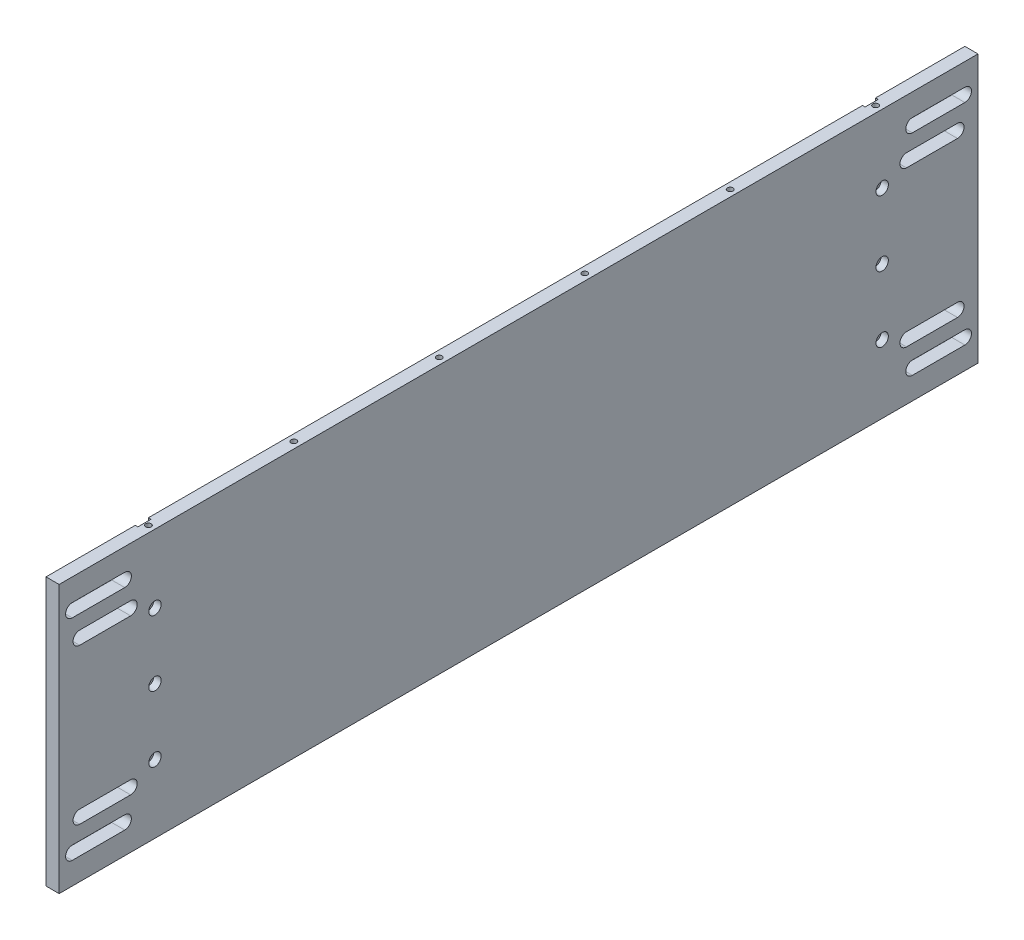
SolidWorks part; units mm, degrees
material "6061 Alloy"
ref_plane "Front Plane" through (0, 0, 0) normal (0, 0, 1) x (1, 0, 0)
ref_plane "Top Plane" through (0, 0, 0) normal (0, 1, 0) x (1, 0, 0)
ref_plane "Right Plane" through (0, 0, 0) normal (1, 0, 0) x (0, 0, -1)
sketch "Sketch1" plane through (0, 0, 0) normal (1, 0, 0) x (0, 0, -1)
  line L1 (0, 0) -> (444.5, 0)
  line L2 (0, 0) -> (0, 129.54)
  line L3 (0, 129.54) -> (444.5, 129.54)
  line L4 (444.5, 0) -> (444.5, 129.54)
  dimension "D1" = 444.5
  dimension "D2" = 129.54
extrude "Boss-Extrude1" add sketch "Sketch1" along normal blind 6.35
hole_wizard "CBORE for #6 Socket Head Cap Screw1" positions "Sketch15" profile "Sketch14" counterbore size "#6" standard "ANSI Inch" end condition through all
sketch "Sketch15" plane through (6.35, 0, 0) normal (1, 0, 0) x (0, 0, -1)
  line L1 (444.5, 129.54) -> (0, 129.54) construction
  line L3 (222.25, 129.54) -> (222.25, 0) construction
  line L4 (0, 0) -> (444.5, 0) construction
  line L6 (46.355, 96.52) -> (46.355, 33.02) construction
  line L8 (398.145, 96.52) -> (398.145, 33.02) construction
  line L9 (444.5, 64.77) -> (0, 64.77) construction
  line L10 (444.5, 0) -> (444.5, 129.54) construction
  line L11 (0, 129.54) -> (0, 0) construction
  point P0 (46.355, 64.77)
  point P8 (398.145, 64.77)
  point P13 (46.355, 96.52)
  point P15 (46.355, 33.02)
  point P17 (398.145, 96.52)
  point P19 (398.145, 33.02)
  dimension "D1" = 175.895
  dimension "D3" = 175.895
  dimension "D4" = 31.75
  dimension "D5" = 31.75
  dimension "D6" = 31.75
  dimension "D7" = 31.75
sketch "Sketch14" plane through (6.35, 64.77, -46.355) normal (0, 1, 0) x (0, 0, -1)
  line L0 (0, 0) -> (0, 6.35)
  line L1 (0, 6.35) -> (1.8288, 6.35)
  line L3 (1.8288, 6.35) -> (1.8288, 3.5052)
  line L4 (1.8288, 3.5052) -> (3, 3.5052)
  line L5 (3, 3.5052) -> (3, 0)
  line L7 (3, 0) -> (0, 0)
  line L11 (0, -6.35) -> (0, 107.95) construction
  dimension "Thru Hole Dia." = 3.6576
  dimension "Thru Hole Depth" = 6.35
  dimension "C'Bore Dia." = 6
  dimension "C'Bore Depth" = 3.5052
sketch "Sketch16" plane through (6.35, 0, 0) normal (1, 0, 0) x (0, 0, -1)
  line L0 (222.25, 129.54) -> (222.25, 0) construction
  line L1 (444.5, 129.54) -> (0, 129.54) construction
  line L2 (0, 0) -> (444.5, 0) construction
  line L3 (6.35, 115.57) -> (31.75, 115.57) construction
  line L4 (0, 129.54) -> (0, 0) construction
  line L5 (0, 64.77) -> (444.5, 64.77) construction
  line L6 (444.5, 0) -> (444.5, 129.54) construction
  line L7 (6.35, 118.7704) -> (31.75, 118.7704)
  line L8 (6.35, 112.3696) -> (31.75, 112.3696)
  line L9 (434.5817, 27.27) -> (409.9183, 27.27) construction
  line L10 (434.5817, 24.095) -> (409.9183, 24.095)
  line L11 (434.5817, 30.445) -> (409.9183, 30.445)
  line L12 (434.5817, 102.27) -> (409.9183, 102.27) construction
  line L13 (434.5817, 105.445) -> (409.9183, 105.445)
  line L14 (434.5817, 99.095) -> (409.9183, 99.095)
  line L15 (6.35, 13.97) -> (31.75, 13.97) construction
  line L16 (6.35, 10.7696) -> (31.75, 10.7696)
  line L17 (6.35, 17.1704) -> (31.75, 17.1704)
  line L18 (438.15, 115.57) -> (412.75, 115.57) construction
  line L19 (438.15, 118.7704) -> (412.75, 118.7704)
  line L20 (438.15, 112.3696) -> (412.75, 112.3696)
  line L21 (9.9183, 102.27) -> (34.5817, 102.27) construction
  line L22 (9.9183, 105.445) -> (34.5817, 105.445)
  line L23 (9.9183, 99.095) -> (34.5817, 99.095)
  line L24 (9.9183, 27.27) -> (34.5817, 27.27) construction
  line L25 (9.9183, 24.095) -> (34.5817, 24.095)
  line L26 (9.9183, 30.445) -> (34.5817, 30.445)
  line L27 (438.15, 13.97) -> (412.75, 13.97) construction
  line L28 (438.15, 10.7696) -> (412.75, 10.7696)
  line L29 (438.15, 17.1704) -> (412.75, 17.1704)
  arc A0 (6.35, 118.7704) -> (6.35, 112.3696) centre (6.35, 115.57) ccw
  arc A1 (31.75, 112.3696) -> (31.75, 118.7704) centre (31.75, 115.57) ccw
  arc A2 (434.5817, 24.095) -> (434.5817, 30.445) centre (434.5817, 27.27) ccw
  arc A3 (409.9183, 30.445) -> (409.9183, 24.095) centre (409.9183, 27.27) ccw
  arc A4 (434.5817, 105.445) -> (434.5817, 99.095) centre (434.5817, 102.27) cw
  arc A5 (409.9183, 99.095) -> (409.9183, 105.445) centre (409.9183, 102.27) cw
  arc A6 (6.35, 10.7696) -> (6.35, 17.1704) centre (6.35, 13.97) cw
  arc A7 (31.75, 17.1704) -> (31.75, 10.7696) centre (31.75, 13.97) cw
  arc A8 (438.15, 118.7704) -> (438.15, 112.3696) centre (438.15, 115.57) cw
  arc A9 (412.75, 112.3696) -> (412.75, 118.7704) centre (412.75, 115.57) cw
  arc A10 (9.9183, 105.445) -> (9.9183, 99.095) centre (9.9183, 102.27) ccw
  arc A11 (34.5817, 99.095) -> (34.5817, 105.445) centre (34.5817, 102.27) ccw
  arc A12 (9.9183, 24.095) -> (9.9183, 30.445) centre (9.9183, 27.27) cw
  arc A13 (34.5817, 30.445) -> (34.5817, 24.095) centre (34.5817, 27.27) cw
  arc A14 (438.15, 10.7696) -> (438.15, 17.1704) centre (438.15, 13.97) ccw
  arc A15 (412.75, 17.1704) -> (412.75, 10.7696) centre (412.75, 13.97) ccw
  point P14 (19.05, 115.57)
  point P20 (422.25, 27.27)
  point P28 (422.25, 102.27)
  point P35 (19.05, 13.97)
  point P42 (425.45, 115.57)
  point P49 (22.25, 102.27)
  point P56 (22.25, 27.27)
  point P63 (425.45, 13.97)
  dimension "D1" = 203.2
  dimension "D2" = 200
  dimension "D3" = 50.8
  dimension "D4" = 37.5
  dimension "D5" = 25.4
  dimension "D6" = 24.6634
extrude "Cut-Extrude1" cut sketch "Sketch16" against normal through all
hole_wizard "Tap Drill for #6-32 Tap1" positions "Sketch17" profile "Sketch18" hole size "#6-32" standard "ANSI Inch"
sketch "Sketch17" plane through (-408.1871, 129.54, -132.107) normal (0, 1, 0) x (0, 0, -1)
  point P0 (-85.752, -59.5721)
  point P3 (-15.394, -59.5721)
  point P6 (54.964, -59.5721)
  point P9 (125.322, -59.5721)
  point P12 (195.68, -59.5721)
  point P15 (266.038, -59.5721)
  point P18 (266.038, -129.9301)
  point P21 (266.038, -200.2881)
  point P24 (266.038, -270.6461)
  point P27 (266.038, -341.0041)
  point P30 (266.038, -411.3621)
  point P33 (195.68, -411.3621)
  point P36 (125.322, -411.3621)
  point P39 (54.964, -411.3621)
  point P42 (-15.394, -411.3621)
  point P45 (-85.752, -411.3621)
  point P48 (-85.752, -341.0041)
  point P51 (-85.752, -270.6461)
  point P54 (-85.752, -200.2881)
  point P57 (-85.752, -129.9301)
sketch "Sketch18" plane through (-348.615, 129.54, -46.355) normal (1, 0, 0) x (0, 0, 1)
  line L0 (0, 0) -> (0, 18.5927)
  line L1 (0, 18.5927) -> (1.3525, 17.78)
  line L2 (1.3525, 17.78) -> (1.3525, 0)
  line L3 (1.3525, 0) -> (0, 0)
  line L4 (0, 18.5927) -> (-1.3525, 17.78) construction
  line L5 (0, -6.35) -> (0, 107.95) construction
  dimension "Hole Dia." = 2.7051
  dimension "Hole Depth" = 17.78
  dimension "Drill Angle" = 118
hole_wizard "Tap Drill for #6-32 Tap2" positions "Sketch19" profile "Sketch20" hole size "#6-32" standard "ANSI Inch"
sketch "Sketch19" plane through (62.7725, 0, -312.3676) normal (0, -1, 0) x (0, 0, -1)
  point P0 (85.752, -411.3621)
  point P3 (15.394, -411.3621)
  point P6 (-54.964, -411.3621)
  point P9 (-125.322, -411.3621)
  point P12 (-195.68, -411.3621)
  point P15 (-266.038, -411.3621)
  point P18 (-266.038, -341.0041)
  point P21 (-266.038, -270.6461)
  point P24 (-266.038, -200.2881)
  point P27 (-266.038, -129.9301)
  point P30 (-266.038, -59.5721)
  point P33 (-195.68, -59.5721)
  point P36 (-125.322, -59.5721)
  point P39 (-54.964, -59.5721)
  point P42 (15.394, -59.5721)
  point P45 (85.752, -59.5721)
  point P48 (85.752, -130.0063)
  point P51 (85.752, -200.3643)
  point P54 (85.752, -270.7223)
  point P57 (85.752, -341.0803)
sketch "Sketch20" plane through (-348.5896, 0, -398.1196) normal (1, 0, 0) x (0, 0, -1)
  line L0 (0, 0) -> (0, 18.5927)
  line L1 (0, 18.5927) -> (1.3525, 17.78)
  line L2 (1.3525, 17.78) -> (1.3525, 0)
  line L3 (1.3525, 0) -> (0, 0)
  line L4 (0, 18.5927) -> (-1.3525, 17.78) construction
  line L5 (0, -6.35) -> (0, 107.95) construction
  dimension "Hole Dia." = 2.7051
  dimension "Hole Depth" = 17.78
  dimension "Drill Angle" = 118
sketch "Sketch21" plane through (0, 0, 0) normal (-1, 0, 0) x (0, 0, 1)
  line L0 (-444.5, 129.54) -> (0, 129.54) construction
  line L1 (-401.32, 0) -> (-394.97, 0)
  line L2 (-401.32, 0) -> (-401.32, 129.54)
  line L3 (-401.32, 129.54) -> (-394.97, 129.54)
  line L4 (-394.97, 0) -> (-394.97, 129.54)
  line L5 (-401.32, 0) -> (-394.97, 129.54) construction
  line L6 (-401.32, 129.54) -> (-394.97, 0) construction
  line L8 (-43.18, 0) -> (-49.53, 0)
  line L9 (-43.18, 0) -> (-43.18, 129.54)
  line L10 (-43.18, 129.54) -> (-49.53, 129.54)
  line L11 (-49.53, 0) -> (-49.53, 129.54)
  line L12 (-43.18, 0) -> (-49.53, 129.54) construction
  line L13 (-43.18, 129.54) -> (-49.53, 0) construction
  point P0 (-398.145, 64.77)
  point P8 (-46.355, 64.77)
  dimension "D1" = 6.35
  dimension "D2" = 6.35
extrude "Cut-Extrude2" cut sketch "Sketch21" against normal blind 1.27
